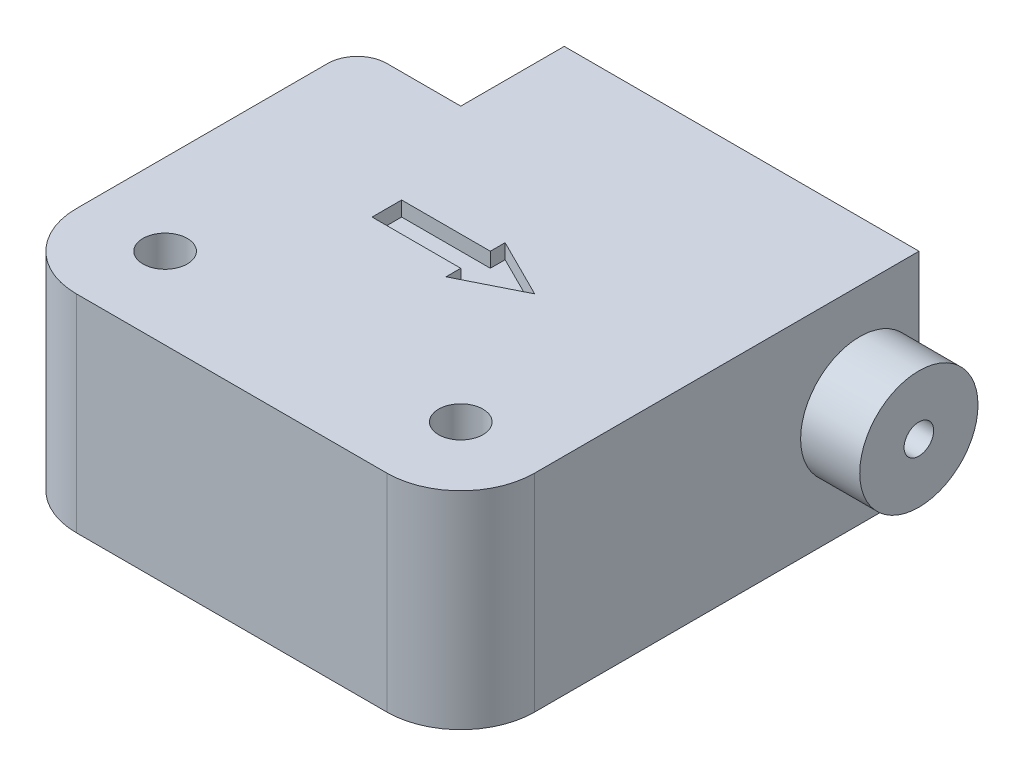
SolidWorks part; units mm, degrees
material "ABS"
ref_plane "Plano frontal" through (0, 0, 0) normal (0, 0, 1) x (1, 0, 0)
ref_plane "Plano superior" through (0, 0, 0) normal (0, 1, 0) x (1, 0, 0)
ref_plane "Plano direito" through (0, 0, 0) normal (1, 0, 0) x (0, 0, -1)
sketch "Esboço1" plane through (0, 0, 0) normal (0, 1, 0) x (1, 0, 0)
  line L0 (0, 0) -> (0, 15.5) construction
  line L1 (-15.5, 15.5) -> (15.5, 15.5)
  line L2 (0, 0) -> (15.5, 0) construction
  line L3 (15.5, -15.5) -> (15.5, 15.5)
  line L4 (-15.5, 15.5) -> (-15.5, -15.5)
  line L5 (-15.5, -15.5) -> (15.5, -15.5)
  line L6 (-8.5, 15.5) -> (-8.5, 8.5)
  line L7 (-8.5, 8.5) -> (-15.5, 8.5)
  line L8 (-15.5, 8.5) -> (-15.5, 15.5)
  circle A0 centre (10, -10) radius 1.5
  circle A1 centre (-10, -10) radius 1.5
  point P5 (0, 15.5)
  point P10 (15.5, 0)
  point P17 (0, 0)
  dimension "D5" = 3
  dimension "D6" = 20
  dimension "D1" = 31
  dimension "D2" = 31
  dimension "D3" = 7
  dimension "D4" = 7
  dimension "D7" = 5.5
extrude "Ressalto-extrusão1" add sketch "Esboço1" along normal blind 14 contours L6 L7 L4 L5 L3 L1 A1 A0
fillet "Filete4" radius 5 2 edges at (-15.5, 7, 15.5) (15.5, 7, 15.5)
fillet "Filete5" radius 2 1 edges at (-15.5, 7, -8.5)
sketch "Esboço5" plane through (15.5, 0, 0) normal (1, 0, 0) x (0, 0, -1)
  line L0 (15.5, 7) -> (-10.5, 7) construction
  line L1 (15.5, 14) -> (15.5, 0) construction
  line L2 (-10.5, 14) -> (-10.5, 0) construction
  circle A0 centre (11.49, 7) radius 4
  dimension "D1" = 8
  dimension "D2" = 4.01
extrude "Ressalto-extrusão4" add sketch "Esboço5" along normal blind 4 contours A0
sketch "Esboço6" plane through (15.5, 0, 0) normal (1, 0, 0) x (0, 0, -1)
  circle A0 centre (11.49, 7) radius 1
  dimension "D1" = 2
extrude "Corte-extrusão3" cut sketch "Esboço6" against normal through all both and the other way through all
sketch "Esboço7" plane through (0, 14, 0) normal (0, 1, 0) x (1, 0, 0)
  line L0 (0, 0) -> (0, -15.5) construction
  line L1 (-10.5, -15.5) -> (10.5, -15.5) construction
  line L2 (-5, 0) -> (0, 0) construction
  line L3 (-5, 1) -> (-5, -1)
  line L4 (-5, -1) -> (1, -1)
  line L5 (1, -1) -> (1, -2)
  line L6 (1, -2) -> (5, 0)
  line L7 (1, 2) -> (5, 0)
  line L8 (1, 1) -> (1, 2)
  line L9 (-5, 1) -> (1, 1)
  point P8 (0, 0)
  point P11 (-5, 0)
  dimension "D1" = 5
  dimension "D2" = 2
  dimension "D3" = 6
  dimension "D4" = 1
  dimension "D5" = 4
extrude "Corte-extrusão4" cut sketch "Esboço7" against normal blind 1
sketch "Esboço9" plane through (0, 0, 0) normal (0, -1, 0) x (1, 0, 0)
  line L0 (-5.1237, -0.9783) -> (0.8763, -0.9783)
  line L1 (0.8763, -0.9783) -> (0.8763, -1.9783)
  line L2 (0.8763, -1.9783) -> (4.8763, 0.0217)
  line L3 (0.8763, 2.0217) -> (4.8763, 0.0217)
  line L4 (0.8763, 1.0217) -> (0.8763, 2.0217)
  line L5 (-5.1237, 1.0217) -> (0.8763, 1.0217)
  line L6 (-5.1237, 1.0217) -> (-5.1237, -0.9783)
extrude "Corte-extrusão5" cut sketch "Esboço9" against normal blind 1
